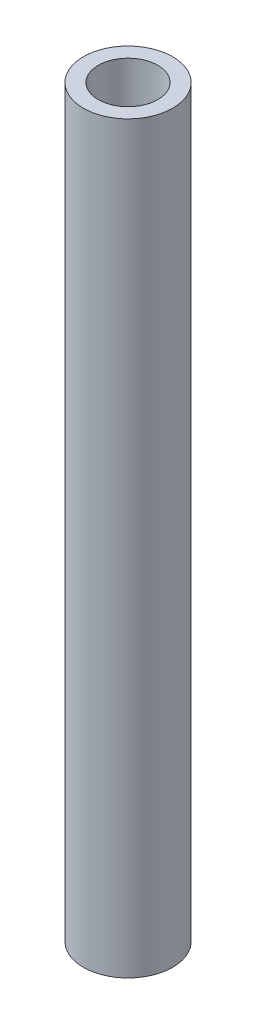
SolidWorks part; units mm, degrees
material "acero"
ref_plane "Alzado" through (0, 0, 0) normal (0, 0, 1) x (1, 0, 0)
ref_plane "Planta" through (0, 0, 0) normal (0, 1, 0) x (1, 0, 0)
ref_plane "Vista lateral" through (0, 0, 0) normal (1, 0, 0) x (0, 0, -1)
sketch "Croquis1" plane through (0, 0, 0) normal (0, 0, 1) x (1, 0, 0)
  line L0 (0, -0.7202) -> (0, 0.7202)
  line L2 (3, -25) -> (-3, -25)
  line L3 (3, -25) -> (3, 25)
  line L4 (3, 25) -> (-3, 25)
  line L5 (-3, -25) -> (-3, 25)
  line L6 (3, -25) -> (-3, 25) construction
  line L7 (3, 25) -> (-3, -25) construction
  line L8 (2, -25) -> (-2, -25)
  line L9 (2, -25) -> (2, 25)
  line L10 (2, 25) -> (-2, 25)
  line L11 (-2, -25) -> (-2, 25)
  line L12 (2, -25) -> (-2, 25) construction
  line L13 (2, 25) -> (-2, -25) construction
  point P1 (0, 0)
  point P3 (0, 0)
  dimension "D1" = 6
  dimension "D2" = 4
  dimension "D3" = 50
revolve "Revolución1" add sketch "Croquis1" angle 360 about L0
